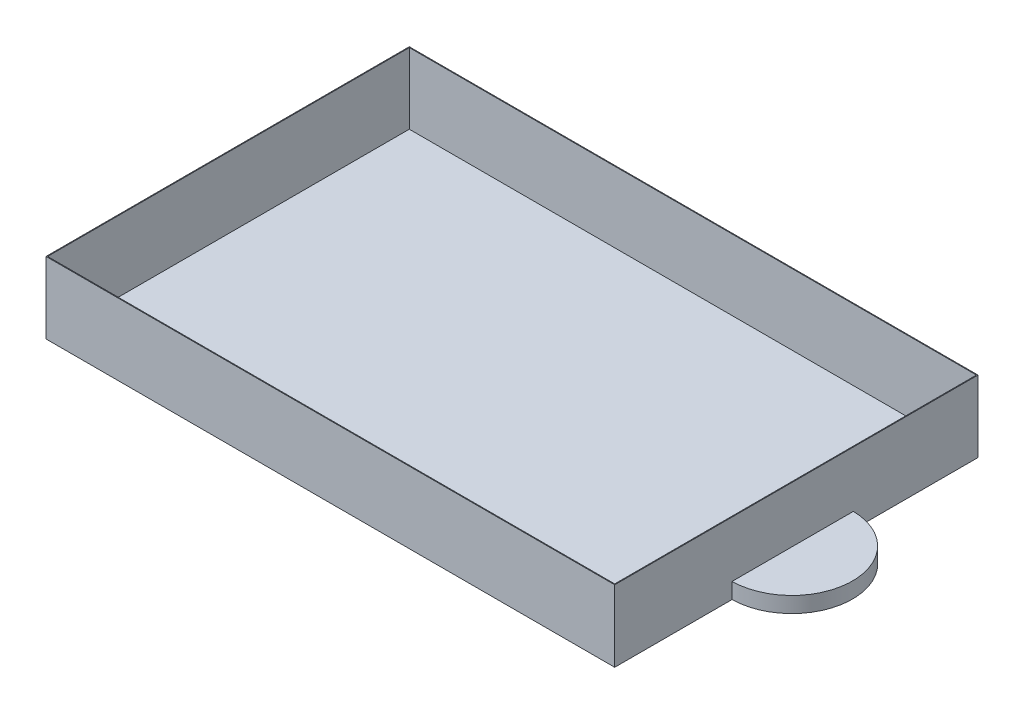
SolidWorks part; units mm, degrees
ref_plane "Alzado" through (0, 0, 0) normal (0, 0, 1) x (1, 0, 0)
ref_plane "Planta" through (0, 0, 0) normal (0, 1, 0) x (1, 0, 0)
ref_plane "Vista lateral" through (0, 0, 0) normal (1, 0, 0) x (0, 0, -1)
sketch "Croquis1" plane through (0, 0, 0) normal (0, 1, 0) x (1, 0, 0)
  line L1 (0, 0) -> (72.4043, 0)
  line L2 (0, 0) -> (0, 46.2519)
  line L3 (0, 46.2519) -> (72.4043, 46.2519)
  line L4 (72.4043, 0) -> (72.4043, 46.2519)
extrude "Saliente-Extruir1" add sketch "Croquis1" along normal blind 9.1
shell "Vaciado2" thickness 0.1
sketch "Croquis2" plane through (0, 0, 0) normal (0, 1, 0) x (1, 0, 0)
  line L0 (72.3043, 0.1) -> (72.3043, 46.1519) construction
  line L5 (0.1, 46.1519) -> (0.1, 0.1)
  line L6 (72.3043, 46.1519) -> (0.1, 46.1519)
  line L7 (72.3043, 0.1) -> (72.3043, 46.1519)
  line L8 (0.1, 0.1) -> (72.3043, 0.1)
  line L11 (72.3043, 14.9365) -> (72.3043, 30.3796)
  arc A0 (72.3043, 30.3796) -> (72.3043, 14.9365) centre (72.3043, 22.6581) cw
  dimension "D1" = 0
extrude "Saliente-Extruir2" add sketch "Croquis2" along normal blind 2
